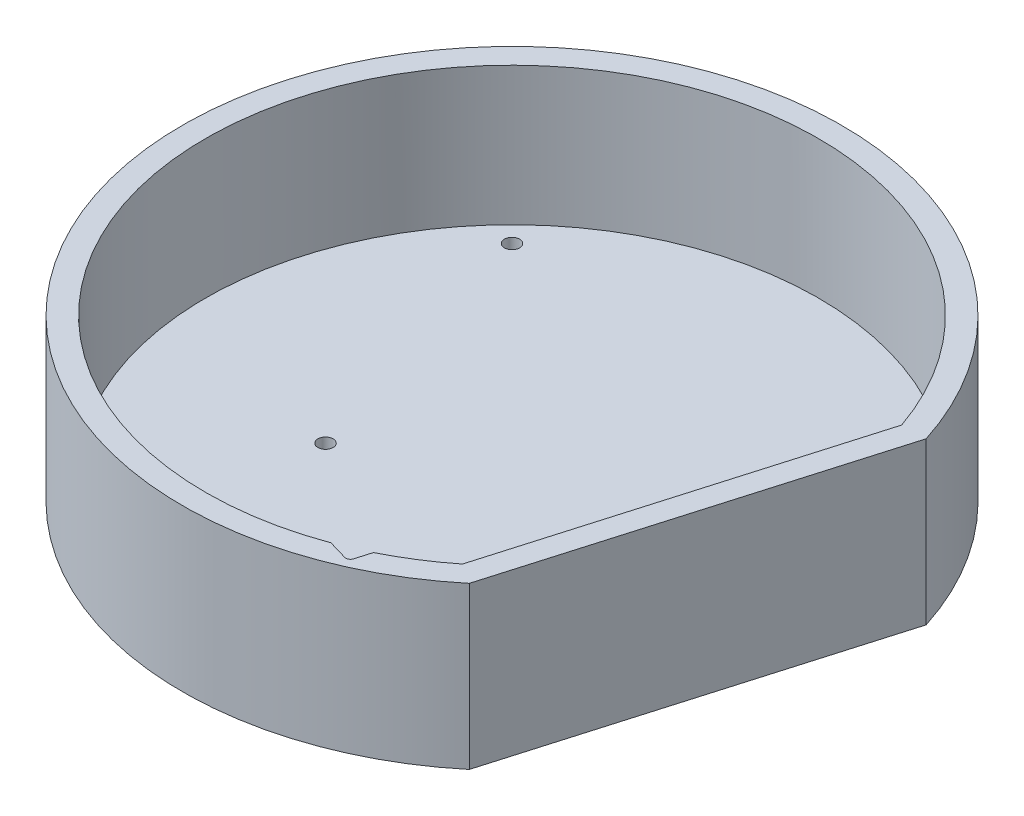
SolidWorks part; units mm, degrees
ref_plane "Front Plane" through (0, 0, 0) normal (0, 0, 1) x (1, 0, 0)
ref_plane "Top Plane" through (0, 0, 0) normal (0, 1, 0) x (1, 0, 0)
ref_plane "Right Plane" through (0, 0, 0) normal (1, 0, 0) x (0, 0, -1)
sketch "Sketch1" plane through (0, 0, 0) normal (0, 1, 0) x (1, 0, 0)
  line L0 (45.7364, -55.017) -> (68.1495, 21.7792)
  line L1 (0, 0) -> (0, 115.6527) construction
  arc A0 (68.1495, 21.7792) -> (45.7364, -55.017) centre (0, 0) ccw
  dimension "D1" = 143.09
  dimension "D2" = 80
  dimension "D3" = 16.27
extrude "Boss-Extrude1" add sketch "Sketch1" along normal blind 5
sketch "Sketch2" plane through (0, 5, 0) normal (0, 1, 0) x (1, 0, 0)
  line L0 (0, 0) -> (50.59, 50.59) construction
  line L1 (0, 0) -> (3.7444, -71.447) construction
  line L2 (0, 0) -> (-50.59, -50.59) construction
  line L3 (0, 0) -> (-50.59, 50.59) construction
  line L4 (41.7547, -41.7547) -> (45.2902, -45.2902) construction
  line L5 (0, 0) -> (0, -71.545) construction
  arc A1 (68.1495, 21.7792) -> (45.7364, -55.017) centre (0, 0) ccw construction
  circle A2 centre (43.5224, 43.5224) radius 1.65
  circle A3 centre (-43.5224, -43.5224) radius 1.65
  circle A4 centre (-43.5224, 43.5224) radius 1.65
  arc A5 (42.3557, -42.3557) -> (44.6891, -44.6891) centre (43.5224, -43.5224) ccw [skipped]
  circle A6 centre (3.2213, -61.4656) radius 1.65
  point P20 (0, 0)
  dimension "D1" = 3.3
  dimension "D2" = 61.55
  dimension "D4" = 3.3
  dimension "D6" = 61.55
  dimension "D5" = 3
  dimension "D3" = 4
extrude "Cut-Extrude1" cut sketch "Sketch2" against normal through all
sketch "Sketch3" plane through (0, 5, 0) normal (0, 1, 0) x (1, 0, 0)
  line L2 (41.3733, -52.1199) -> (62.9131, 21.6837)
  line L3 (41.3733, -52.1199) -> (62.9131, 21.6837)
  line L5 (45.7364, -55.017) -> (68.1495, 21.7792)
  line L6 (45.7364, -55.017) -> (68.1495, 21.7792)
  arc A2 (62.9131, 21.6837) -> (41.3733, -52.1199) centre (0, 0) ccw
  arc A3 (62.9131, 21.6837) -> (41.3733, -52.1199) centre (0, 0) ccw
  arc A6 (68.1495, 21.7792) -> (45.7364, -55.017) centre (0, 0) ccw
  arc A7 (68.1495, 21.7792) -> (45.7364, -55.017) centre (0, 0) ccw
  dimension "D1" = 5
  dimension "D2" = 0
extrude "Boss-Extrude3" add sketch "Sketch3" along normal blind 30
ref_plane "Plane1" through (42.5437, 0, 12.4165) normal (-0.96, 0, -0.2802) x (-0.2802, 0, 0.96)
ref_plane "Plane2" through (-10.7699, 0, 36.9018) normal (0.2802, 0, -0.96) x (0, -1, 0)
sketch "Sketch4" plane through (-10.7699, 0, 36.9018) normal (0.2802, 0, -0.96) x (0, -1, 0)
  line L0 (-19, -41.5685) -> (-35, -41.5685) construction
  line L1 (-19, -45.0685) -> (-35, -45.0685)
  line L2 (-19, -38.0685) -> (-35, -38.0685)
  line L3 (16.5, -44.3185) -> (-16.5, -44.3185) construction
  arc A0 (-19, -45.0685) -> (-19, -38.0685) centre (-19, -41.5685) ccw
  arc A1 (-35, -38.0685) -> (-35, -45.0685) centre (-35, -41.5685) ccw
  point P2 (-27, -41.5685)
  dimension "D1" = 3.5
  dimension "D2" = 14
  dimension "D3" = 0
  dimension "D4" = 2.75
extrude "Cut-Extrude2" cut sketch "Sketch4" against normal blind 15
fillet "Fillet1" radius 1 2 edges at (26.5293, 15.9211, 63.4135) (28.2913, 27, 63.9277)
sketch "Sketch5" plane through (0, 5, 0) normal (0, 1, 0) x (1, 0, 0)
  line L1 (47.1664, 3.4228) -> (37.921, -28.2557) construction
  line L3 (5.0693, -41.5245) -> (-26.6091, -32.2791) construction
  circle A0 centre (26.5691, -29.6734) radius 1.65
  circle A1 centre (-26.2282, -14.2644) radius 1.65
  dimension "D1" = 17.4
  dimension "D2" = 3.3
  dimension "D4" = 3.3
  dimension "D5" = 10.5
  dimension "D6" = 65.5
  dimension "D3" = 17.4
extrude "Cut-Extrude3" cut sketch "Sketch5" against normal through all
